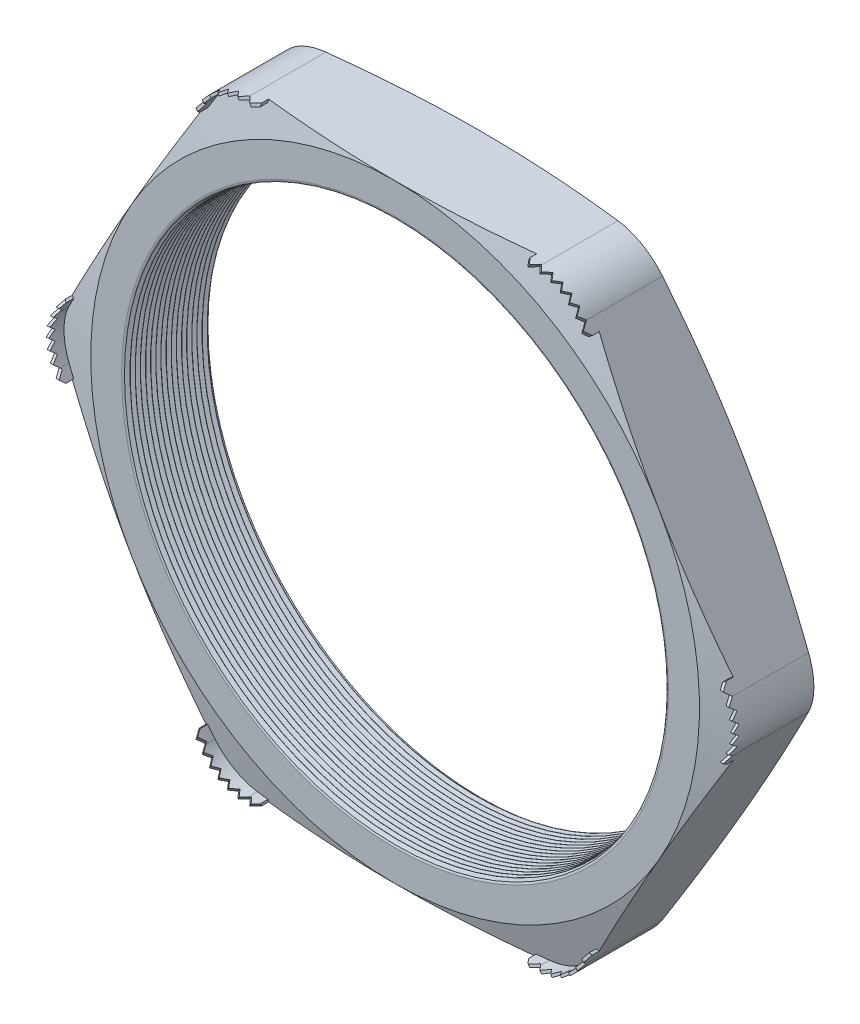
SolidWorks part; units mm, degrees
ref_plane "Front Plane" through (0, 0, 0) normal (0, 0, 1) x (1, 0, 0)
ref_plane "Top Plane" through (0, 0, 0) normal (0, 1, 0) x (1, 0, 0)
ref_plane "Right Plane" through (0, 0, 0) normal (1, 0, 0) x (0, 0, -1)
sketch "Sketch1" plane through (0, 0, 0) normal (0, 0, 1) x (1, 0, 0)
  line L1 (-20.8239, 0) -> (-10.4119, -18.034)
  line L2 (-10.4119, -18.034) -> (10.4119, -18.034)
  line L3 (10.4119, -18.034) -> (20.8239, 0)
  line L4 (20.8239, 0) -> (10.4119, 18.034)
  line L5 (10.4119, 18.034) -> (-10.4119, 18.034)
  line L6 (-10.4119, 18.034) -> (-20.8239, 0)
  circle A0 centre (0, 0) radius 18.034 construction
  circle A1 centre (0, 0) radius 16.002
  dimension "TS" = 32.004
  dimension "H" = 36.068
extrude "Extrude1" add sketch "Sketch1" along normal blind 5.08
fillet "Fillet1" radius 3.048 6 edges at (-10.4119, 18.034, 2.54) (-20.8239, 0, 2.54) (-10.4119, -18.034, 2.54) (10.4119, -18.034, 2.54) (20.8239, 0, 2.54) (10.4119, 18.034, 2.54)
sketch "Sketch2" plane through (0, 0, 5.08) normal (0, 0, 1) x (1, 0, 0)
  line L0 (-8.6522, 18.034) -> (-7.941, 18.034)
  line L1 (8.6522, 18.034) -> (-8.6522, 18.034) construction
  line L2 (-11.2918, 16.51) -> (-11.6474, 15.8941)
  line L3 (-11.2918, 16.51) -> (-19.944, 1.524) construction
  line L4 (-8.6522, 17.8816) -> (-7.941, 17.8816)
  line L5 (-11.1598, 16.4338) -> (-11.5154, 15.8179)
  line L6 (-11.6474, 15.8941) -> (-11.5154, 15.8179)
  line L7 (-7.941, 18.034) -> (-7.941, 17.8816)
  arc A0 (-8.6522, 17.8816) -> (-11.1598, 16.4338) centre (-8.6522, 14.986) ccw
  arc A1 (-8.6522, 18.034) -> (-11.2918, 16.51) centre (-8.6522, 14.986) ccw construction
  arc A4 (-8.6522, 18.034) -> (-11.2918, 16.51) centre (-8.6522, 14.986) ccw
  dimension "D1" = 0.7112
  dimension "D2" = 0.7112
  dimension "OFFSET" = 0.1524
fillet "Fillet3" radius 0.2032 2 edges at (16.002, 0, 0) (16.002, 0, 5.08)
sketch "Sketch3" plane through (0, 0, 0) normal (0, 1, 0) x (1, 0, 0)
  line L0 (-16.002, -5.08) -> (-16.002, -4.7867)
  line L2 (-16.002, -4.7867) -> (-16.256, -4.9334)
  line L3 (-16.256, -4.9334) -> (-16.002, -5.08)
  line L4 (-16.002, -0.2032) -> (-16.002, -4.8768) construction
  line L5 (-11.2918, -5.08) -> (-19.944, -5.08) construction
  dimension "D1" = 60
  dimension "D2" = 60
  dimension "D3" = 0.254
revolve "Cut-Revolve1" cut sketch "Sketch3" angle 360 about axis through (0, 0, 5.08) along (0, 0, -1)
pattern_linear "LPattern1" count 17 spacing 0.3048 along (0, 0, -1) of "Cut-Revolve1"
sketch "Sketch4" plane through (0, 0, 0) normal (0, 0, -1) x (-1, 0, 0)
  line L0 (-19.944, 1.524) -> (-11.2918, 16.51) construction
  circle A0 centre (0, 0) radius 18.034
extrude "Cut-Extrude1" cut sketch "Sketch4" against normal through all draft 75 flip side to cut
sketch "Sketch5" plane through (0, 0, 5.08) normal (0, 0, 1) x (1, 0, 0)
  line L0 (8.6522, 18.034) -> (-8.6522, 18.034) construction
  circle A0 centre (0, 0) radius 18.034
extrude "Cut-Extrude2" cut sketch "Sketch5" against normal through all draft 75 flip side to cut
extrude "Extrude2" add sketch "Sketch2" along normal blind 0.8636 and the other way up to next
ref_plane "Plane1" through (-9.7282, 16.8497, 0) normal (0.5, -0.866, 0) x (0.866, 0.5, 0)
sketch "Sketch7" plane through (-9.7282, 16.8497, 0) normal (0.5, -0.866, 0) x (0.866, 0.5, 0)
  line L0 (-2.1399, 5.0368) -> (-1.8351, 5.3995)
  line L1 (-2.1399, 4.6323) -> (-2.1399, 5.9436) construction
  line L2 (0, 1.3136) -> (0, 4.0135) construction
  line L4 (-1.8351, 5.3995) -> (-1.5303, 5.0368)
  line L5 (-0.6096, 5.3995) -> (-0.3048, 5.0368)
  line L6 (-1.2192, 5.3995) -> (-0.9144, 5.0368)
  line L7 (-0.3048, 5.0368) -> (0, 5.3995)
  line L8 (0, 5.3995) -> (0.3048, 5.0368)
  line L10 (0.6096, 5.3995) -> (0.9144, 5.0368)
  line L11 (1.2192, 5.3995) -> (1.524, 5.0368)
  line L12 (-1.5303, 5.0368) -> (-1.2192, 5.3995)
  line L13 (-0.9144, 5.0368) -> (-0.6096, 5.3995)
  line L14 (0.3048, 5.0368) -> (0.6096, 5.3995)
  line L15 (1.8351, 5.3995) -> (2.1399, 5.0368)
  line L16 (2.1399, 4.6323) -> (2.1399, 5.9436) construction
  line L17 (-2.1399, 5.0368) -> (-2.1399, 5.9436)
  line L19 (-2.1399, 5.9436) -> (2.1399, 5.9436)
  line L20 (2.1399, 5.9436) -> (2.1399, 5.0368)
  line L23 (0.9144, 5.0368) -> (1.2192, 5.3995)
  line L25 (1.524, 5.0368) -> (1.8351, 5.3995)
  dimension "D1" = 0.9068
  dimension "D2" = 0.5441
  dimension "D3" = 0.3048
extrude "Cut-Extrude4" cut sketch "Sketch7" against normal through all
pattern_circular "CirPattern1" count 6 over 360 about axis through (0, 0, 0) along (0, 0, 1) of "Extrude2"
pattern_circular "CirPattern2" count 6 over 360 about axis through (0, 0, 0) along (0, 0, 1) of "Cut-Extrude4"
